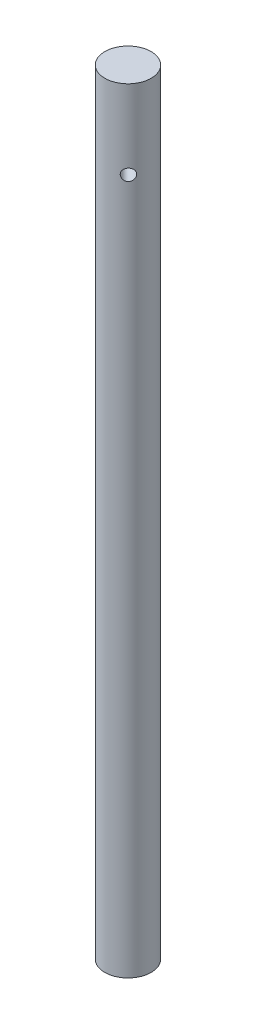
SolidWorks part; units mm, degrees
ref_plane "Front Plane" through (0, 0, 0) normal (0, 0, 1) x (1, 0, 0)
ref_plane "Top Plane" through (0, 0, 0) normal (0, 1, 0) x (1, 0, 0)
ref_plane "Right Plane" through (0, 0, 0) normal (1, 0, 0) x (0, 0, -1)
sketch "Sketch1" plane through (0, 0, 0) normal (0, 1, 0) x (1, 0, 0)
  circle A0 centre (0, 0) radius 2.99
extrude "Boss-Extrude1" add sketch "Sketch1" along normal blind 100
sketch "Sketch2" plane through (0, 100, 0) normal (0, 1, 0) x (1, 0, 0)
  point P0 (0, 0)
ref_plane "Plane1" through (0, 0, 12.54) normal (0, 0, 1) x (1, 0, 0)
sketch "Sketch3" plane through (0, 0, 12.54) normal (0, 0, 1) x (1, 0, 0)
  point P0 (0, 90)
  dimension "D1" = 10
hole_wizard "Ø1.5mm Dowel Hole5" positions "3DSketch4" profile "Sketch7" hole size "Ø1.5" standard "ANSI Metric"
sketch3d "3DSketch4"
  point P0 (2.1442, 89.8183, 2.0838)
sketch "Sketch7" plane through (2.1442, 89.8183, 2.0838) normal (0, 1, 0) x (0.6969, 0, -0.7171)
  line L0 (0, 0) -> (0, 20.4506)
  line L1 (0, 20.4506) -> (0.75, 20)
  line L2 (0.75, 20) -> (0.75, 0)
  line L5 (0.75, 0) -> (0, 0)
  line L10 (0, 20.4506) -> (-0.75, 20) construction
  line L11 (0, -6.35) -> (0, 107.95) construction
  dimension "Hole Dia." = 1.5
  dimension "Hole Depth" = 20
  dimension "Drill Angle" = 118
